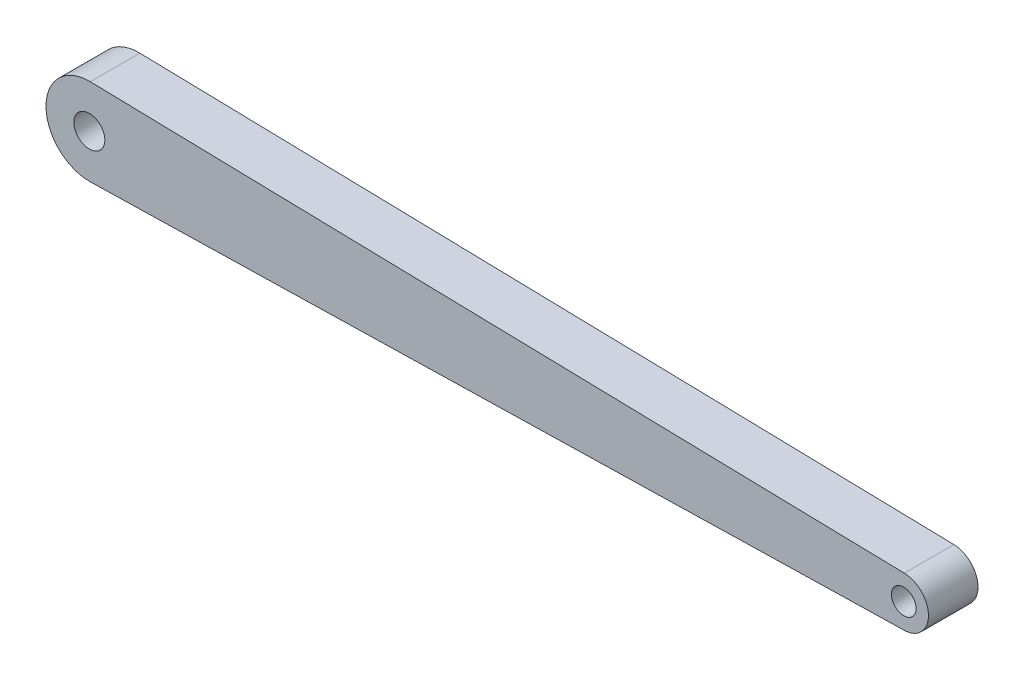
SolidWorks part; units mm, degrees
ref_plane "Front Plane" through (0, 0, 0) normal (0, 0, 1) x (1, 0, 0)
ref_plane "Top Plane" through (0, 0, 0) normal (0, 1, 0) x (1, 0, 0)
ref_plane "Right Plane" through (0, 0, 0) normal (1, 0, 0) x (0, 0, -1)
sketch "Sketch1" plane through (0, 0, 0) normal (0, 0, 1) x (1, 0, 0)
  line L0 (-1315, 0) -> (0, 0) construction
  line L1 (-1313.403, 69.9818) -> (0.9125, 39.9896)
  line L2 (-1313.403, -69.9818) -> (0.9125, -39.9896)
  circle A0 centre (0, 0) radius 20
  circle A1 centre (-1315, 0) radius 25
  arc A2 (-1313.403, 69.9818) -> (-1313.403, -69.9818) centre (-1315, 0) ccw
  arc A3 (0.9125, 39.9896) -> (0.9125, -39.9896) centre (0, 0) cw
  dimension "D2" = 50
  dimension "D3" = 40
  dimension "D4" = 70
  dimension "D5" = 40
  dimension "D1" = 1315
extrude "Boss-Extrude1" add sketch "Sketch1" along normal mid plane 80
